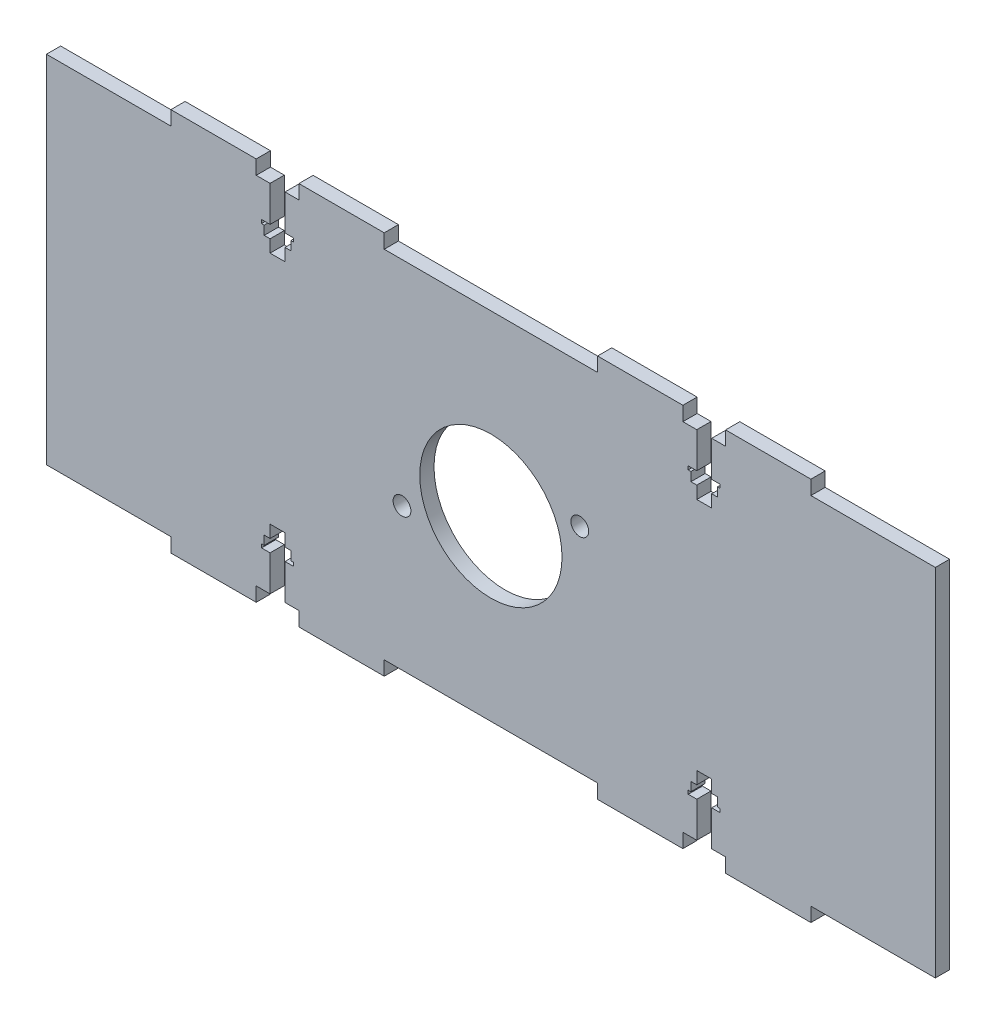
SolidWorks part; units mm, degrees
ref_plane "Front Plane" through (0, 0, 0) normal (0, 0, 1) x (1, 0, 0)
ref_plane "Top Plane" through (0, 0, 0) normal (0, 1, 0) x (1, 0, 0)
ref_plane "Right Plane" through (0, 0, 0) normal (1, 0, 0) x (0, 0, -1)
sketch "Sketch1" plane through (0, 0, 0) normal (0, 0, 1) x (1, 0, 0)
  line L1 (-125, 50) -> (125, 50)
  line L2 (-125, 50) -> (-125, -50)
  line L3 (-125, -50) -> (125, -50)
  line L4 (125, 50) -> (125, -50)
  line L5 (-125, 50) -> (125, -50) construction
  line L6 (-125, -50) -> (125, 50) construction
  point P0 (0, 0)
  dimension "D1" = 250
  dimension "D2" = 100
extrude "Boss-Extrude1" add sketch "Sketch1" along normal blind 4
sketch "Sketch2" plane through (0, -50, 0) normal (0, -1, 0) x (1, 0, 0)
  line L0 (-125, 4) -> (125, 4) construction
  line L1 (-66, 4) -> (-90, 4)
  line L2 (-66, 4) -> (-66, 0)
  line L3 (-66, 0) -> (-90, 0)
  line L4 (-90, 4) -> (-90, 0)
  line L5 (-125, 0) -> (125, 0) construction
  line L7 (-54, 4) -> (-30, 4)
  line L8 (-54, 4) -> (-54, 0)
  line L9 (-54, 0) -> (-30, 0)
  line L10 (-30, 4) -> (-30, 0)
  line L11 (-125, 4) -> (-125, 0) construction
  line L12 (0, 0) -> (0, 4) construction
  line L13 (30, 4) -> (30, 0)
  line L14 (54, 0) -> (30, 0)
  line L15 (54, 4) -> (54, 0)
  line L16 (54, 4) -> (30, 4)
  line L17 (90, 4) -> (90, 0)
  line L18 (66, 0) -> (90, 0)
  line L19 (66, 4) -> (66, 0)
  line L20 (66, 4) -> (90, 4)
  dimension "D1" = 24
  dimension "D2" = 35
  dimension "D3" = 12
  dimension "D4" = 24
extrude "Boss-Extrude2" add sketch "Sketch2" along normal blind 4
mirror "Mirror1" about plane through (0, 0, 0) normal (0, 1, 0) of "Boss-Extrude2"
sketch "Sketch3" plane through (0, 0, 0) normal (0, 0, -1) x (-1, 0, 0)
  line L0 (-62.1, -50) -> (-57.9, -50)
  line L1 (-62.1, -50) -> (-62.1, -40)
  line L2 (-62.1, -33) -> (-57.9, -33)
  line L3 (-57.9, -50) -> (-57.9, -40)
  line L4 (-60, -50) -> (-60, -33) construction
  line L5 (-63.75, -36.5) -> (-62.1, -36.5)
  line L6 (-63.75, -36.5) -> (-63.75, -39)
  line L7 (-57.9, -36.5) -> (-57.9, -33)
  line L8 (-56.25, -36.5) -> (-56.25, -39)
  line L9 (-64.5, -39) -> (-64.5, -40)
  line L10 (-55.5, -40) -> (-57.9, -40)
  line L12 (0, 0) -> (0, -50) construction
  line L13 (30, -50) -> (-30, -50) construction
  line L14 (0, 0) -> (-125, 0) construction
  line L15 (-125, -50) -> (-125, 50) construction
  line L16 (-57.9, -40) -> (-55.5, -40)
  line L17 (-55.5, -39) -> (-55.5, -40)
  line L18 (-55.5, -39) -> (-56.25, -39)
  line L19 (-57.9, -36.5) -> (-57.9, -33)
  line L20 (-56.25, -39) -> (-55.5, -39)
  line L21 (-62.1, -36.5) -> (-63.75, -36.5)
  line L22 (-63.75, -39) -> (-64.5, -39)
  line L23 (-57.9, -36.5) -> (-56.25, -36.5)
  line L24 (-62.1, -36.5) -> (-62.1, -33)
  line L25 (-62.1, -40) -> (-64.5, -40)
  line L26 (-63.75, -36.5) -> (-63.75, -39)
  line L27 (-62.1, -36.5) -> (-62.1, -33)
  line L28 (-64.5, -39) -> (-63.75, -39)
  line L29 (-64.5, -39) -> (-64.5, -40)
  line L30 (-64.5, -40) -> (-62.1, -40)
  line L31 (-55.5, -39) -> (-55.5, -40)
  line L32 (-56.25, -36.5) -> (-56.25, -39)
  line L33 (-56.25, -36.5) -> (-57.9, -36.5)
  line L34 (-62.1, -50) -> (-62.1, -40)
  line L35 (-57.9, -50) -> (-57.9, -40)
  line L36 (-62.1, -50) -> (-62.1, -40)
  line L37 (-57.9, -50) -> (-57.9, -40)
  line L38 (-63.75, -36.5) -> (-62.1, -36.5)
  line L39 (-63.75, -36.5) -> (-63.75, -39)
  line L40 (-64.5, -39) -> (-64.5, -40)
  line L41 (-55.5, -40) -> (-57.9, -40)
  line L42 (-55.5, -39) -> (-55.5, -40)
  line L43 (-55.5, -39) -> (-56.25, -39)
  line L44 (-57.9, -36.5) -> (-57.9, -33)
  line L45 (-56.25, -36.5) -> (-56.25, -39)
  line L46 (-57.9, -40) -> (-55.5, -40)
  line L47 (-57.9, -36.5) -> (-57.9, -33)
  line L48 (-62.1, -36.5) -> (-63.75, -36.5)
  line L49 (-56.25, -39) -> (-55.5, -39)
  line L50 (-57.9, -36.5) -> (-56.25, -36.5)
  line L51 (-63.75, -39) -> (-64.5, -39)
  line L52 (-62.1, -36.5) -> (-62.1, -33)
  line L53 (-64.5, -39) -> (-63.75, -39)
  line L54 (-64.5, -39) -> (-64.5, -40)
  line L55 (-62.1, -40) -> (-64.5, -40)
  line L56 (-64.5, -40) -> (-62.1, -40)
  line L57 (-55.5, -39) -> (-55.5, -40)
  line L58 (-63.75, -36.5) -> (-63.75, -39)
  line L59 (-62.1, -36.5) -> (-62.1, -33)
  line L60 (-56.25, -36.5) -> (-56.25, -39)
  line L61 (-56.25, -36.5) -> (-57.9, -36.5)
  line L62 (-62.1, -50) -> (-62.1, -40)
  line L63 (-57.9, -50) -> (-57.9, -40)
  line L64 (-54, -50) -> (-66, -50) construction
  line L65 (60, -50) -> (60, -33) construction
  line L66 (57.9, -50) -> (57.9, -40)
  line L67 (62.1, -50) -> (62.1, -40)
  line L68 (56.25, -36.5) -> (57.9, -36.5)
  line L69 (56.25, -36.5) -> (56.25, -39)
  line L70 (62.1, -36.5) -> (62.1, -33)
  line L71 (63.75, -36.5) -> (63.75, -39)
  line L72 (55.5, -39) -> (55.5, -40)
  line L73 (64.5, -40) -> (62.1, -40)
  line L74 (62.1, -40) -> (64.5, -40)
  line L75 (64.5, -39) -> (64.5, -40)
  line L76 (64.5, -39) -> (63.75, -39)
  line L77 (62.1, -36.5) -> (62.1, -33)
  line L78 (63.75, -39) -> (64.5, -39)
  line L79 (57.9, -36.5) -> (56.25, -36.5)
  line L80 (56.25, -39) -> (55.5, -39)
  line L81 (62.1, -36.5) -> (63.75, -36.5)
  line L82 (57.9, -36.5) -> (57.9, -33)
  line L83 (57.9, -40) -> (55.5, -40)
  line L84 (56.25, -36.5) -> (56.25, -39)
  line L85 (57.9, -36.5) -> (57.9, -33)
  line L86 (55.5, -39) -> (56.25, -39)
  line L87 (55.5, -39) -> (55.5, -40)
  line L88 (55.5, -40) -> (57.9, -40)
  line L89 (64.5, -39) -> (64.5, -40)
  line L90 (63.75, -36.5) -> (63.75, -39)
  line L91 (63.75, -36.5) -> (62.1, -36.5)
  line L92 (57.9, -50) -> (57.9, -40)
  line L93 (62.1, -50) -> (62.1, -40)
  line L94 (57.9, -50) -> (57.9, -40)
  line L95 (62.1, -50) -> (62.1, -40)
  line L96 (56.25, -36.5) -> (57.9, -36.5)
  line L97 (56.25, -36.5) -> (56.25, -39)
  line L98 (55.5, -39) -> (55.5, -40)
  line L99 (64.5, -40) -> (62.1, -40)
  line L100 (64.5, -39) -> (64.5, -40)
  line L101 (64.5, -39) -> (63.75, -39)
  line L102 (62.1, -36.5) -> (62.1, -33)
  line L103 (63.75, -36.5) -> (63.75, -39)
  line L104 (62.1, -40) -> (64.5, -40)
  line L105 (62.1, -36.5) -> (62.1, -33)
  line L106 (57.9, -36.5) -> (56.25, -36.5)
  line L107 (63.75, -39) -> (64.5, -39)
  line L108 (62.1, -36.5) -> (63.75, -36.5)
  line L109 (56.25, -39) -> (55.5, -39)
  line L110 (57.9, -36.5) -> (57.9, -33)
  line L111 (55.5, -39) -> (56.25, -39)
  line L112 (55.5, -39) -> (55.5, -40)
  line L113 (57.9, -40) -> (55.5, -40)
  line L114 (55.5, -40) -> (57.9, -40)
  line L115 (64.5, -39) -> (64.5, -40)
  line L116 (56.25, -36.5) -> (56.25, -39)
  line L117 (57.9, -36.5) -> (57.9, -33)
  line L118 (63.75, -36.5) -> (63.75, -39)
  line L119 (63.75, -36.5) -> (62.1, -36.5)
  line L120 (57.9, -50) -> (57.9, -40)
  line L121 (62.1, -33) -> (57.9, -33)
  line L122 (62.1, -50) -> (62.1, -40)
  line L123 (62.1, -50) -> (57.9, -50)
  line L124 (60, 50) -> (60, 33) construction
  line L125 (-60, 50) -> (-60, 33) construction
  line L126 (62.1, 50) -> (57.9, 50)
  line L127 (62.1, 50) -> (62.1, 40)
  line L128 (62.1, 33) -> (57.9, 33)
  line L129 (57.9, 50) -> (57.9, 40)
  line L130 (63.75, 36.5) -> (62.1, 36.5)
  line L131 (63.75, 36.5) -> (63.75, 39)
  line L132 (57.9, 36.5) -> (57.9, 33)
  line L133 (56.25, 36.5) -> (56.25, 39)
  line L134 (64.5, 39) -> (64.5, 40)
  line L135 (55.5, 40) -> (57.9, 40)
  line L136 (57.9, 40) -> (55.5, 40)
  line L137 (55.5, 39) -> (55.5, 40)
  line L138 (55.5, 39) -> (56.25, 39)
  line L139 (57.9, 36.5) -> (57.9, 33)
  line L140 (56.25, 39) -> (55.5, 39)
  line L141 (62.1, 36.5) -> (63.75, 36.5)
  line L142 (63.75, 39) -> (64.5, 39)
  line L143 (57.9, 36.5) -> (56.25, 36.5)
  line L144 (62.1, 36.5) -> (62.1, 33)
  line L145 (62.1, 40) -> (64.5, 40)
  line L146 (63.75, 36.5) -> (63.75, 39)
  line L147 (62.1, 36.5) -> (62.1, 33)
  line L148 (64.5, 39) -> (63.75, 39)
  line L149 (64.5, 39) -> (64.5, 40)
  line L150 (64.5, 40) -> (62.1, 40)
  line L151 (55.5, 39) -> (55.5, 40)
  line L152 (56.25, 36.5) -> (56.25, 39)
  line L153 (56.25, 36.5) -> (57.9, 36.5)
  line L154 (62.1, 50) -> (62.1, 40)
  line L155 (57.9, 50) -> (57.9, 40)
  line L156 (62.1, 50) -> (62.1, 40)
  line L157 (57.9, 50) -> (57.9, 40)
  line L158 (63.75, 36.5) -> (62.1, 36.5)
  line L159 (63.75, 36.5) -> (63.75, 39)
  line L160 (64.5, 39) -> (64.5, 40)
  line L161 (55.5, 40) -> (57.9, 40)
  line L162 (55.5, 39) -> (55.5, 40)
  line L163 (55.5, 39) -> (56.25, 39)
  line L164 (57.9, 36.5) -> (57.9, 33)
  line L165 (56.25, 36.5) -> (56.25, 39)
  line L166 (57.9, 40) -> (55.5, 40)
  line L167 (57.9, 36.5) -> (57.9, 33)
  line L168 (62.1, 36.5) -> (63.75, 36.5)
  line L169 (56.25, 39) -> (55.5, 39)
  line L170 (57.9, 36.5) -> (56.25, 36.5)
  line L171 (63.75, 39) -> (64.5, 39)
  line L172 (62.1, 36.5) -> (62.1, 33)
  line L173 (64.5, 39) -> (63.75, 39)
  line L174 (64.5, 39) -> (64.5, 40)
  line L175 (62.1, 40) -> (64.5, 40)
  line L176 (64.5, 40) -> (62.1, 40)
  line L177 (55.5, 39) -> (55.5, 40)
  line L178 (63.75, 36.5) -> (63.75, 39)
  line L179 (62.1, 36.5) -> (62.1, 33)
  line L180 (56.25, 36.5) -> (56.25, 39)
  line L181 (56.25, 36.5) -> (57.9, 36.5)
  line L182 (62.1, 50) -> (62.1, 40)
  line L183 (57.9, 50) -> (57.9, 40)
  line L184 (-57.9, 50) -> (-57.9, 40)
  line L185 (-62.1, 50) -> (-62.1, 40)
  line L186 (-56.25, 36.5) -> (-57.9, 36.5)
  line L187 (-56.25, 36.5) -> (-56.25, 39)
  line L188 (-62.1, 36.5) -> (-62.1, 33)
  line L189 (-63.75, 36.5) -> (-63.75, 39)
  line L190 (-55.5, 39) -> (-55.5, 40)
  line L191 (-64.5, 40) -> (-62.1, 40)
  line L192 (-62.1, 40) -> (-64.5, 40)
  line L193 (-64.5, 39) -> (-64.5, 40)
  line L194 (-64.5, 39) -> (-63.75, 39)
  line L195 (-62.1, 36.5) -> (-62.1, 33)
  line L196 (-63.75, 39) -> (-64.5, 39)
  line L197 (-57.9, 36.5) -> (-56.25, 36.5)
  line L198 (-56.25, 39) -> (-55.5, 39)
  line L199 (-62.1, 36.5) -> (-63.75, 36.5)
  line L200 (-57.9, 36.5) -> (-57.9, 33)
  line L201 (-57.9, 40) -> (-55.5, 40)
  line L202 (-56.25, 36.5) -> (-56.25, 39)
  line L203 (-57.9, 36.5) -> (-57.9, 33)
  line L204 (-55.5, 39) -> (-56.25, 39)
  line L205 (-55.5, 39) -> (-55.5, 40)
  line L206 (-55.5, 40) -> (-57.9, 40)
  line L207 (-64.5, 39) -> (-64.5, 40)
  line L208 (-63.75, 36.5) -> (-63.75, 39)
  line L209 (-63.75, 36.5) -> (-62.1, 36.5)
  line L210 (-57.9, 50) -> (-57.9, 40)
  line L211 (-62.1, 50) -> (-62.1, 40)
  line L212 (-57.9, 50) -> (-57.9, 40)
  line L213 (-62.1, 50) -> (-62.1, 40)
  line L214 (-56.25, 36.5) -> (-57.9, 36.5)
  line L215 (-56.25, 36.5) -> (-56.25, 39)
  line L216 (-55.5, 39) -> (-55.5, 40)
  line L217 (-64.5, 40) -> (-62.1, 40)
  line L218 (-64.5, 39) -> (-64.5, 40)
  line L219 (-64.5, 39) -> (-63.75, 39)
  line L220 (-62.1, 36.5) -> (-62.1, 33)
  line L221 (-63.75, 36.5) -> (-63.75, 39)
  line L222 (-62.1, 40) -> (-64.5, 40)
  line L223 (-62.1, 36.5) -> (-62.1, 33)
  line L224 (-57.9, 36.5) -> (-56.25, 36.5)
  line L225 (-63.75, 39) -> (-64.5, 39)
  line L226 (-62.1, 36.5) -> (-63.75, 36.5)
  line L227 (-56.25, 39) -> (-55.5, 39)
  line L228 (-57.9, 36.5) -> (-57.9, 33)
  line L229 (-55.5, 39) -> (-56.25, 39)
  line L230 (-55.5, 39) -> (-55.5, 40)
  line L231 (-57.9, 40) -> (-55.5, 40)
  line L232 (-55.5, 40) -> (-57.9, 40)
  line L233 (-64.5, 39) -> (-64.5, 40)
  line L234 (-56.25, 36.5) -> (-56.25, 39)
  line L235 (-57.9, 36.5) -> (-57.9, 33)
  line L236 (-63.75, 36.5) -> (-63.75, 39)
  line L237 (-63.75, 36.5) -> (-62.1, 36.5)
  line L238 (-57.9, 50) -> (-57.9, 40)
  line L239 (-62.1, 33) -> (-57.9, 33)
  line L240 (-62.1, 50) -> (-62.1, 40)
  line L241 (-62.1, 50) -> (-57.9, 50)
  dimension "D1" = 4.2
  dimension "D2" = 17
  dimension "D3" = 7.5
  dimension "D4" = 2.5
  dimension "D5" = 9
  dimension "D6" = 1
  dimension "D7" = 11
extrude "Cut-Extrude1" cut sketch "Sketch3" against normal blind 10
sketch "Sketch4" plane through (0, 0, 0) normal (0, 0, -1) x (-1, 0, 0)
  circle A0 centre (0, 0) radius 20
  circle A1 centre (-25, 10) radius 2.5
  circle A2 centre (25, -10) radius 2.5
  dimension "D1" = 40
  dimension "D6" = 5
  dimension "D7" = 5
  dimension "D2" = 25
  dimension "D3" = 25
  dimension "D4" = 10
  dimension "D5" = 10
extrude "Cut-Extrude2" cut sketch "Sketch4" against normal blind 10
